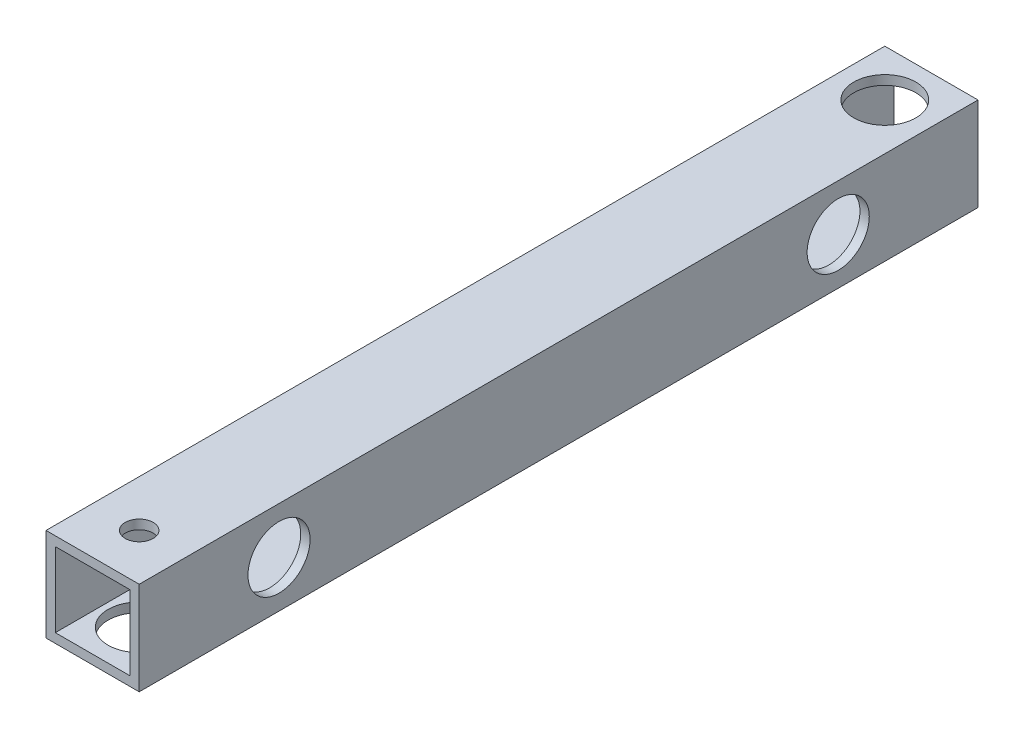
SolidWorks part; units mm, degrees
material "6063-T5"
ref_plane "正面" through (0, 0, 0) normal (0, 0, 1) x (1, 0, 0)
ref_plane "平面" through (0, 0, 0) normal (0, 1, 0) x (1, 0, 0)
ref_plane "右側面" through (0, 0, 0) normal (1, 0, 0) x (0, 0, -1)
sketch "ｽｹｯﾁ1" plane through (0, 0, 0) normal (0, 0, 1) x (1, 0, 0)
  line L1 (-7.5, -7.5) -> (7.5, -7.5)
  line L2 (-7.5, -7.5) -> (-7.5, 7.5)
  line L3 (-7.5, 7.5) -> (7.5, 7.5)
  line L4 (7.5, -7.5) -> (7.5, 7.5)
  line L5 (-7.5, -7.5) -> (7.5, 7.5) construction
  line L6 (-7.5, 7.5) -> (7.5, -7.5) construction
  line L7 (-6, -6) -> (6, -6)
  line L8 (-6, -6) -> (-6, 6)
  line L9 (-6, 6) -> (6, 6)
  line L10 (6, -6) -> (6, 6)
  line L11 (-6, -6) -> (6, 6) construction
  line L12 (-6, 6) -> (6, -6) construction
  point P0 (0, 0)
  point P6 (0, 0)
  dimension "D1" = 1.5
  dimension "D2" = 15
  dimension "D3" = 15
extrude "ﾎﾞｽ - 押し出し1" add sketch "ｽｹｯﾁ1" along normal blind 135
sketch "ｽｹｯﾁ2" plane through (7.5, 0, 0) normal (1, 0, 0) x (0, 0, -1)
  line L0 (-135, -7.5) -> (0, -7.5) construction
  line L2 (-135, -7.5) -> (-135, 7.5) construction
  circle A4 centre (-112.5, 0) radius 2.7
  circle A8 centre (-22.5, 0) radius 2.7
  dimension "D1" = 5.4
  dimension "D2" = 22.5
  dimension "D3" = 7.5
  dimension "D4" = 90
  dimension "D9" = 2
extrude "ｶｯﾄ - 押し出し1" cut sketch "ｽｹｯﾁ2" against normal blind 25
sketch "ｽｹｯﾁ3" plane through (0, 7.5, 0) normal (0, 1, 0) x (1, 0, 0)
  line L2 (7.5, -135) -> (7.5, 0) construction
  circle A1 centre (0, -7.5) radius 2.7
  circle A6 centre (0, -127.5) radius 2.25
  dimension "D2" = 120
  dimension "D3" = 5.4
  dimension "D9" = 7.5
  dimension "D11" = 7.5
  dimension "D4" = 7.5
  dimension "D5" = 4.5
extrude "ｶｯﾄ - 押し出し2" cut sketch "ｽｹｯﾁ3" against normal blind 25
sketch "ｽｹｯﾁ4" plane through (0, 7.5, 0) normal (0, 1, 0) x (1, 0, 0)
  circle A0 centre (0, -7.5) radius 5
  dimension "D2" = 10
extrude "ｶｯﾄ - 押し出し3" cut sketch "ｽｹｯﾁ4" against normal blind 10
sketch "ｽｹｯﾁ5" plane through (7.5, 0, 0) normal (1, 0, 0) x (0, 0, -1)
  circle A0 centre (-22.5, 0) radius 5
  circle A1 centre (-112.5, 0) radius 5
  dimension "D1" = 10
  dimension "D2" = 10
extrude "ｶｯﾄ - 押し出し4" cut sketch "ｽｹｯﾁ5" against normal blind 10
sketch "ｽｹｯﾁ6" plane through (0, -7.5, 0) normal (0, -1, 0) x (-1, 0, 0)
  circle A0 centre (0, -127.5) radius 5
  dimension "D1" = 10
extrude "ｶｯﾄ - 押し出し5" cut sketch "ｽｹｯﾁ6" against normal blind 10
